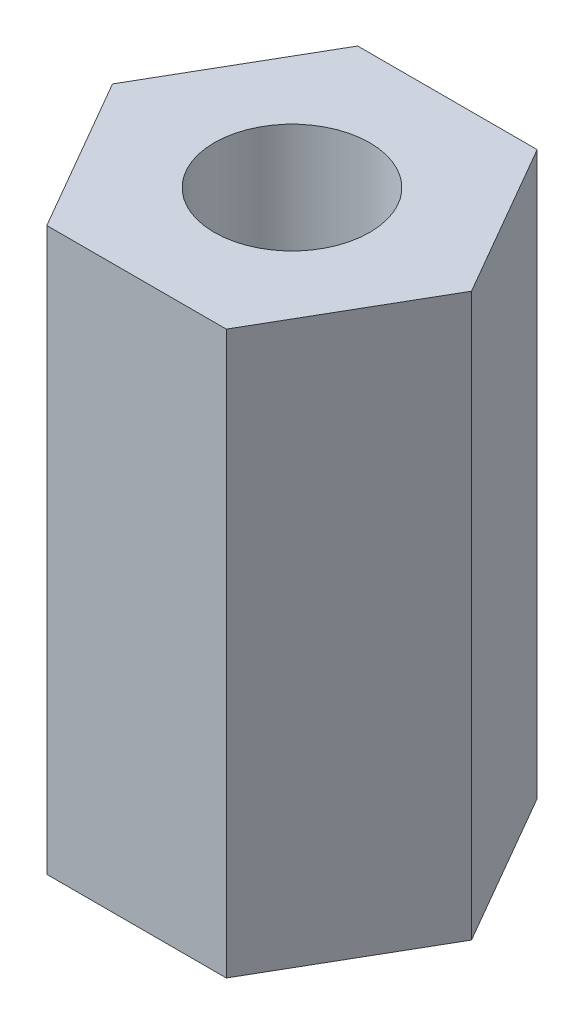
SolidWorks part; units mm, degrees
ref_plane "前视基准面" through (0, 0, 0) normal (0, 0, 1) x (1, 0, 0)
ref_plane "上视基准面" through (0, 0, 0) normal (0, 1, 0) x (1, 0, 0)
ref_plane "右视基准面" through (0, 0, 0) normal (1, 0, 0) x (0, 0, -1)
sketch "草图1" plane through (0, 0, 0) normal (0, 1, 0) x (1, 0, 0)
  line L7 (2.3094, 0) -> (1.1547, 2)
  line L8 (1.1547, 2) -> (-1.1547, 2)
  line L9 (-1.1547, 2) -> (-2.3094, 0)
  line L10 (-2.3094, 0) -> (-1.1547, -2)
  line L11 (-1.1547, -2) -> (1.1547, -2)
  line L12 (1.1547, -2) -> (2.3094, 0)
  circle A0 centre (0, 0) radius 2 construction
  circle A1 centre (0, 0) radius 1
  dimension "D2" = 2
  dimension "D1" = 4
extrude "凸台-拉伸1" add sketch "草图1" along normal blind 7.23
